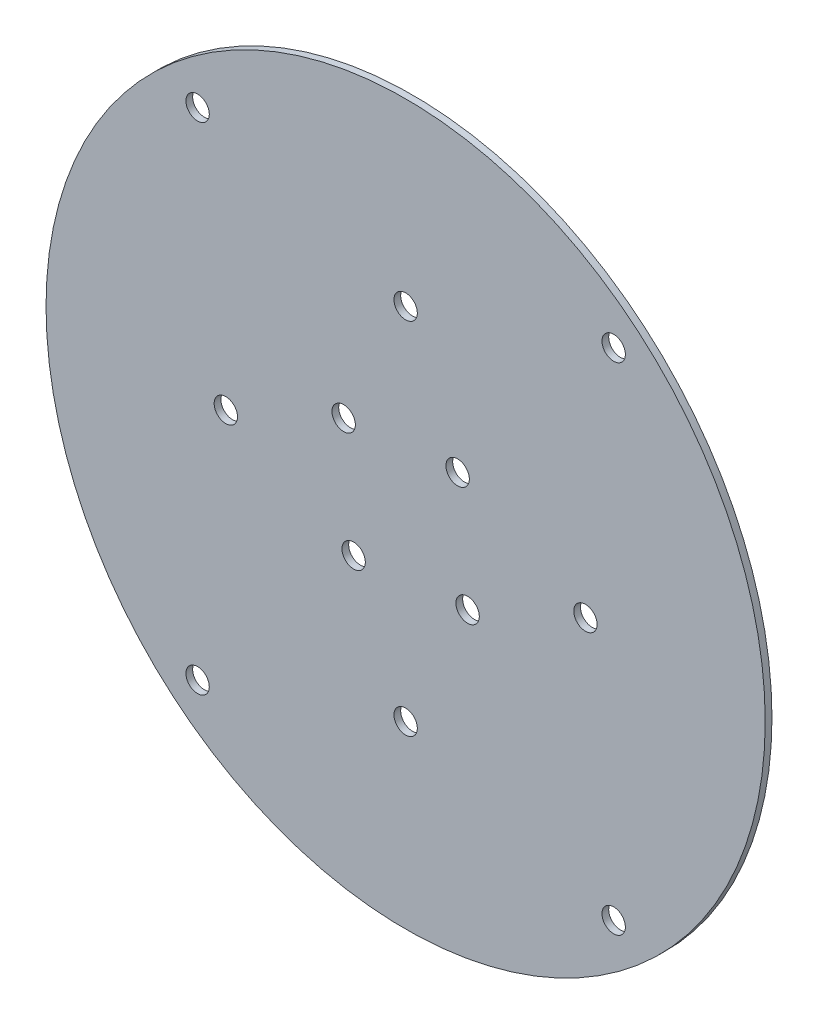
SolidWorks part; units mm, degrees
ref_plane "Front Plane" through (0, 0, 0) normal (0, 0, 1) x (1, 0, 0)
ref_plane "Top Plane" through (0, 0, 0) normal (0, 1, 0) x (1, 0, 0)
ref_plane "Right Plane" through (0, 0, 0) normal (1, 0, 0) x (0, 0, -1)
sketch "Sketch1" plane through (0, 0, 0) normal (0, 0, 1) x (1, 0, 0)
  line L0 (-46.2807, -55.1552) -> (46.2807, 55.1552) construction
  line L1 (46.2807, -55.1552) -> (-46.2807, 55.1552) construction
  line L2 (0, 0) -> (0, 40) construction
  circle A0 centre (0, 0) radius 80
  circle A1 centre (-46.2807, 55.1552) radius 2.6
  circle A2 centre (-46.2807, -55.1552) radius 2.6
  circle A3 centre (46.2807, -55.1552) radius 2.6
  circle A4 centre (46.2807, 55.1552) radius 2.6
  circle A5 centre (0, 40) radius 2.6
  circle A6 centre (40, 0) radius 2.6
  circle A7 centre (0, -40) radius 2.6
  circle A8 centre (-40, 0) radius 2.6
  point P6 (0, 0)
  point P9 (0, 0)
  dimension "D1" = 160
  dimension "D5" = 5.2
  dimension "D8" = 4
  dimension "D9" = 5.2
  dimension "D2" = 80
  dimension "D3" = 144
  dimension "D4" = 144
  dimension "D6" = 40
  dimension "D7" = 40
extrude "Boss-Extrude1" add sketch "Sketch1" along normal blind 1.5
sketch "Sketch2" plane through (0, 0, 0) normal (0, 0, -1) x (-1, 0, 0)
  line L0 (0, 0) -> (-11.5702, 13.7888) construction
  line L1 (0, 0) -> (0, 16.8193) construction
  circle A0 centre (-11.5702, 13.7888) radius 2.6
  dimension "D2" = 5.2
  dimension "D1" = 18
extrude "Cut-Extrude1" cut sketch "Sketch2" against normal blind 10
pattern_circular "CirPattern1" count 4 over 360 about axis through (0, 0, 0) along (0, 0, 1) of "Cut-Extrude1"
